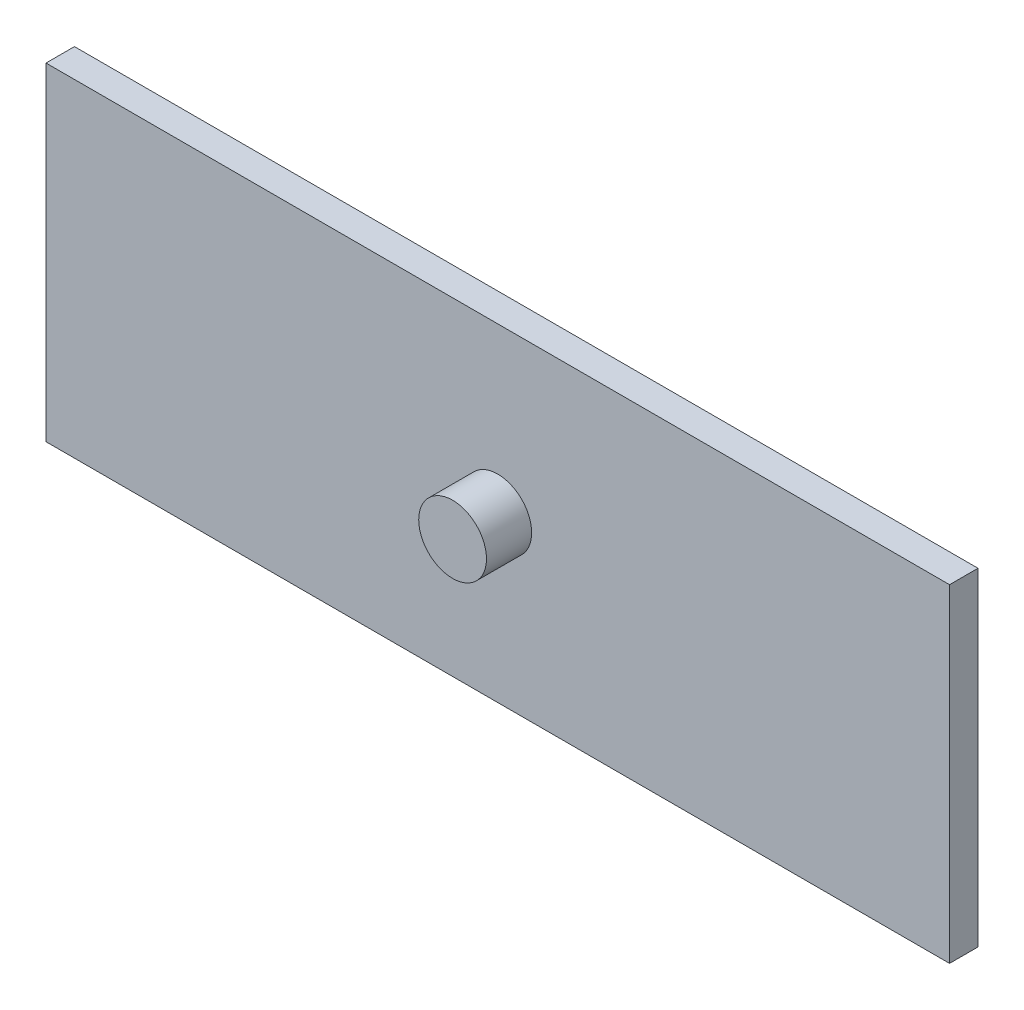
SolidWorks part; units mm, degrees
ref_plane "Front Plane" through (0, 0, 0) normal (0, 0, 1) x (1, 0, 0)
ref_plane "Top Plane" through (0, 0, 0) normal (0, 1, 0) x (1, 0, 0)
ref_plane "Right Plane" through (0, 0, 0) normal (1, 0, 0) x (0, 0, -1)
sketch "Sketch1" plane through (0, 0, 0) normal (0, 0, 1) x (1, 0, 0)
  line L1 (0, 0) -> (200, 0)
  line L2 (0, 0) -> (0, 72.6)
  line L3 (0, 72.6) -> (200, 72.6)
  line L4 (200, 0) -> (200, 72.6)
  dimension "D1" = 72.6
  dimension "D2" = 200
extrude "Boss-Extrude1" add sketch "Sketch1" along normal blind 6.3
sketch "Sketch2" plane through (0, 0, 6.3) normal (0, 0, 1) x (1, 0, 0)
  line L0 (200, 72.6) -> (0, 72.6) construction
  line L1 (0, 72.6) -> (0, 0) construction
  circle A0 centre (100, 36.3) radius 7.5
  point P2 (0, 0)
  point P5 (100, 72.6)
  point P6 (0, 0)
  point P9 (0, 36.3)
  dimension "D1" = 15
extrude "Boss-Extrude2" add sketch "Sketch2" along normal blind 10
